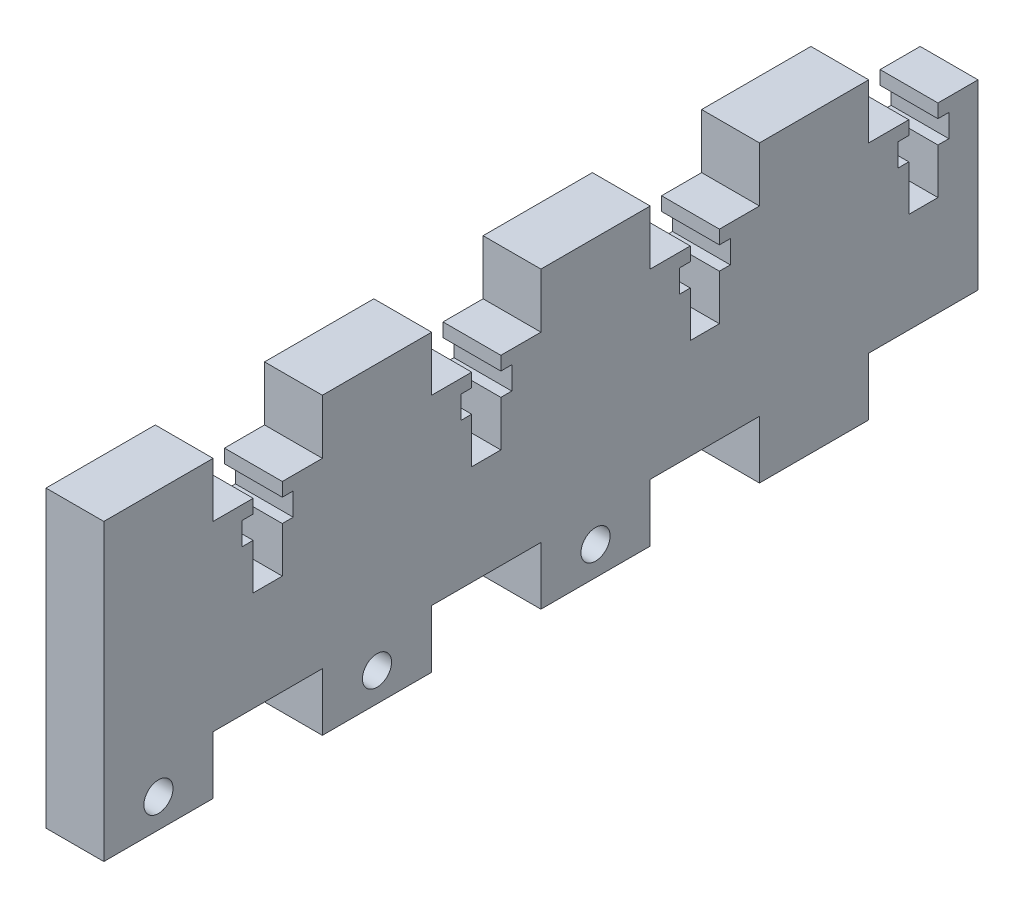
SolidWorks part; units mm, degrees
material "Acrylic (Medium-high impact)"
ref_plane "Front Plane" through (0, 0, 0) normal (0, 0, 1) x (1, 0, 0)
ref_plane "Top Plane" through (0, 0, 0) normal (0, 1, 0) x (1, 0, 0)
ref_plane "Right Plane" through (0, 0, 0) normal (1, 0, 0) x (0, 0, -1)
sketch "Sketch1" plane through (0, 0, 0) normal (1, 0, 0) x (0, 0, -1)
  line L1 (-48, -10) -> (48, -10)
  line L2 (-48, -10) -> (-48, 10)
  line L3 (-48, 10) -> (48, 10)
  line L4 (48, -10) -> (48, 10)
  line L5 (-48, -10) -> (48, 10) construction
  line L6 (-48, 10) -> (48, -10) construction
  point P0 (0, 0)
  dimension "D1" = 20
  dimension "D2" = 96
extrude "Boss-Extrude1" add sketch "Sketch1" along normal blind 6.35
sketch "Sketch2" plane through (6.35, 0, 0) normal (1, 0, 0) x (0, 0, -1)
  line L0 (-24, 10) -> (-12, 10)
  line L1 (-48, 10) -> (-36, 10)
  line L2 (-48, 10) -> (-48, 16)
  line L3 (-48, 16) -> (-36, 16)
  line L4 (-36, 10) -> (-36, 16)
  line L5 (-24, 10) -> (-24, 16)
  line L6 (-24, 16) -> (-12, 16)
  line L7 (-12, 10) -> (-12, 16)
  line L8 (0, 10) -> (12, 10)
  line L9 (0, 10) -> (0, 16)
  line L10 (0, 16) -> (12, 16)
  line L11 (12, 10) -> (12, 16)
  line L12 (24, 10) -> (36, 10)
  line L13 (24, 10) -> (24, 16)
  line L14 (24, 16) -> (36, 16)
  line L15 (36, 10) -> (36, 16)
  line L16 (12, -10) -> (0, -10)
  line L17 (36, -10) -> (24, -10)
  line L18 (36, -10) -> (36, -16.35)
  line L19 (36, -16.35) -> (24, -16.35)
  line L20 (24, -10) -> (24, -16.35)
  line L21 (12, -10) -> (12, -16.35)
  line L22 (12, -16.35) -> (0, -16.35)
  line L23 (0, -10) -> (0, -16.35)
  line L24 (-12, -10) -> (-24, -10)
  line L25 (-12, -10) -> (-12, -16.35)
  line L26 (-12, -16.35) -> (-24, -16.35)
  line L27 (-24, -10) -> (-24, -16.35)
  line L28 (-36, -10) -> (-48, -10)
  line L29 (-36, -10) -> (-36, -16.35)
  line L30 (-36, -16.35) -> (-48, -16.35)
  line L31 (-48, -10) -> (-48, -16.35)
  dimension "D1" = 6
  dimension "D2" = 12
  dimension "D4" = 24
  dimension "D5" = 6.35
  dimension "D7" = 24
  dimension "D3" = 4
  dimension "D6" = 4
extrude "Boss-Extrude2" add sketch "Sketch2" against normal blind 6.35
sketch "Sketch3" plane through (6.35, 0, 0) normal (1, 0, 0) x (0, 0, -1)
  line L0 (-24, 10) -> (-36, 10) construction
  line L1 (-24, 10) -> (-36, 10) construction
  line L2 (-30, 10) -> (-30, 0) construction
  line L3 (-31.6, 10) -> (-31.6, 8.5)
  line L4 (-31.6, 8.5) -> (-32.8, 8.5)
  line L5 (-32.8, 8.5) -> (-32.8, 6)
  line L6 (-32.8, 6) -> (-31.6, 6)
  line L7 (-31.6, 6) -> (-31.6, 1)
  line L8 (-31.6, 1) -> (-28.4, 1)
  line L9 (-31.6, 10) -> (-28.4, 10)
  line L10 (-28.4, 6) -> (-28.4, 1)
  line L11 (-27.2, 6) -> (-28.4, 6)
  line L12 (-27.2, 8.5) -> (-27.2, 6)
  line L13 (-28.4, 8.5) -> (-27.2, 8.5)
  line L14 (-28.4, 10) -> (-28.4, 8.5)
  line L15 (-7.6, 10) -> (-7.6, 8.5)
  line L16 (-7.6, 10) -> (-4.4, 10)
  line L17 (-4.4, 10) -> (-4.4, 8.5)
  line L18 (-4.4, 8.5) -> (-3.2, 8.5)
  line L19 (-3.2, 8.5) -> (-3.2, 6)
  line L20 (-3.2, 6) -> (-4.4, 6)
  line L21 (-4.4, 6) -> (-4.4, 1)
  line L22 (-7.6, 1) -> (-4.4, 1)
  line L23 (-7.6, 6) -> (-7.6, 1)
  line L24 (-8.8, 6) -> (-7.6, 6)
  line L25 (-8.8, 8.5) -> (-8.8, 6)
  line L26 (-7.6, 8.5) -> (-8.8, 8.5)
  line L27 (16.4, 10) -> (16.4, 8.5)
  line L28 (16.4, 10) -> (19.6, 10)
  line L29 (19.6, 10) -> (19.6, 8.5)
  line L30 (19.6, 8.5) -> (20.8, 8.5)
  line L31 (20.8, 8.5) -> (20.8, 6)
  line L32 (20.8, 6) -> (19.6, 6)
  line L33 (19.6, 6) -> (19.6, 1)
  line L34 (16.4, 1) -> (19.6, 1)
  line L35 (16.4, 6) -> (16.4, 1)
  line L36 (15.2, 6) -> (16.4, 6)
  line L37 (15.2, 8.5) -> (15.2, 6)
  line L38 (16.4, 8.5) -> (15.2, 8.5)
  line L39 (40.4, 10) -> (40.4, 8.5)
  line L40 (40.4, 10) -> (43.6, 10)
  line L41 (43.6, 10) -> (43.6, 8.5)
  line L42 (43.6, 8.5) -> (44.8, 8.5)
  line L43 (44.8, 8.5) -> (44.8, 6)
  line L44 (44.8, 6) -> (43.6, 6)
  line L45 (43.6, 6) -> (43.6, 1)
  line L46 (40.4, 1) -> (43.6, 1)
  line L47 (40.4, 6) -> (40.4, 1)
  line L48 (39.2, 6) -> (40.4, 6)
  line L49 (39.2, 8.5) -> (39.2, 6)
  line L50 (40.4, 8.5) -> (39.2, 8.5)
  line L51 (-42, -13.175) -> (-36, -13.175) construction
  line L52 (-36, -16.35) -> (-36, -10) construction
  line L53 (-42, -13.175) -> (-42, -16.35) construction
  line L54 (-48, -16.35) -> (-36, -16.35) construction
  circle A0 centre (-42, -13.175) radius 1.6
  circle A1 centre (-18, -13.175) radius 1.6
  circle A2 centre (6, -13.175) radius 1.6
  point P12 (-30, 1)
  dimension "D8" = 3.2
  dimension "D1" = 1.6
  dimension "D2" = 2.8
  dimension "D3" = 9
  dimension "D4" = 2.5
  dimension "D5" = 1.5
  dimension "D7" = 24
  dimension "D10" = 24
  dimension "D6" = 4
  dimension "D9" = 3
extrude "Cut-Extrude1" cut sketch "Sketch3" against normal blind 10
